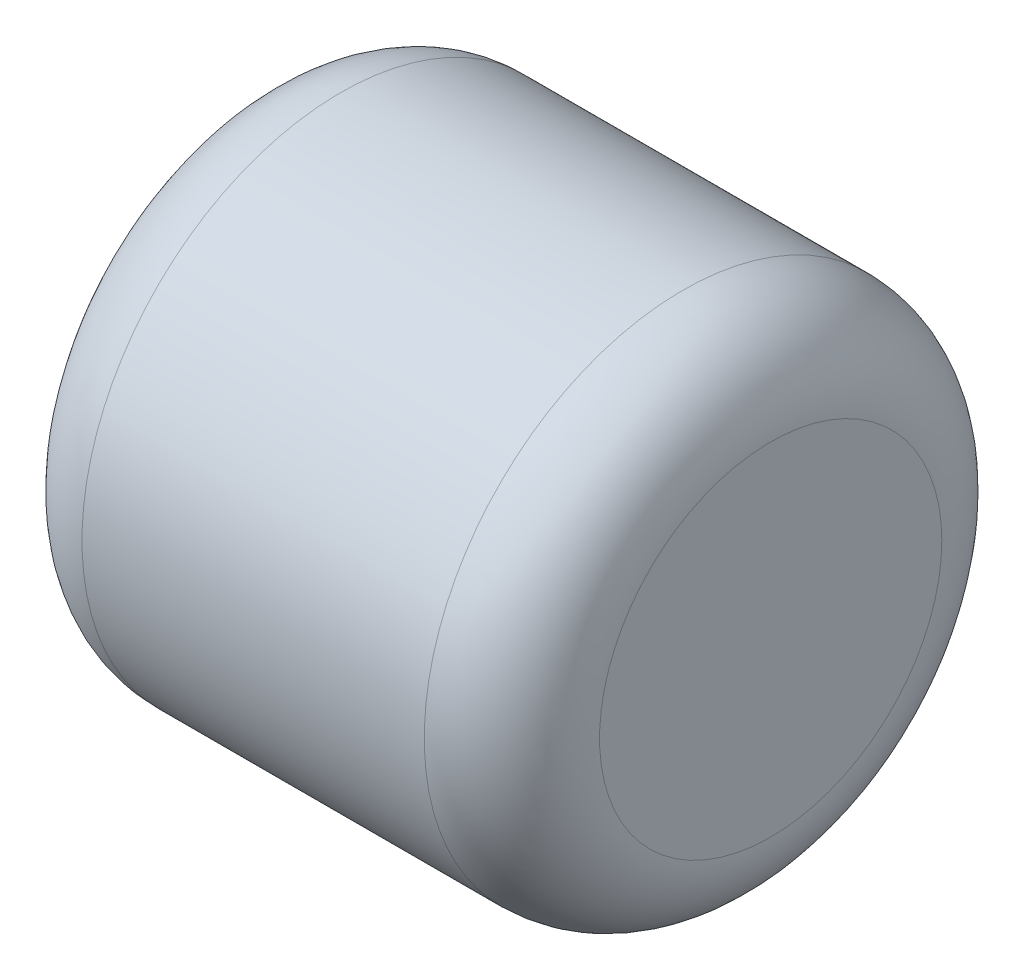
SolidWorks part; units mm, degrees
material "SmCo 26 (17:2)"
ref_plane "Front" through (0, 0, 0) normal (0, 0, 1) x (1, 0, 0)
ref_plane "Top" through (0, 0, 0) normal (0, 1, 0) x (1, 0, 0)
ref_plane "Right" through (0, 0, 0) normal (1, 0, 0) x (0, 0, -1)
sketch "Sketch1" plane through (0, 0, 0) normal (1, 0, 0) x (0, 0, -1)
  circle A0 centre (0, 0) radius 1.5
  dimension "D1" = 3
extrude "Extrude1" add sketch "Sketch1" along normal blind 3
fillet "Fillet1" radius 0.508 2 edges at (0, 0, -1.5) (3, 0, -1.5)
